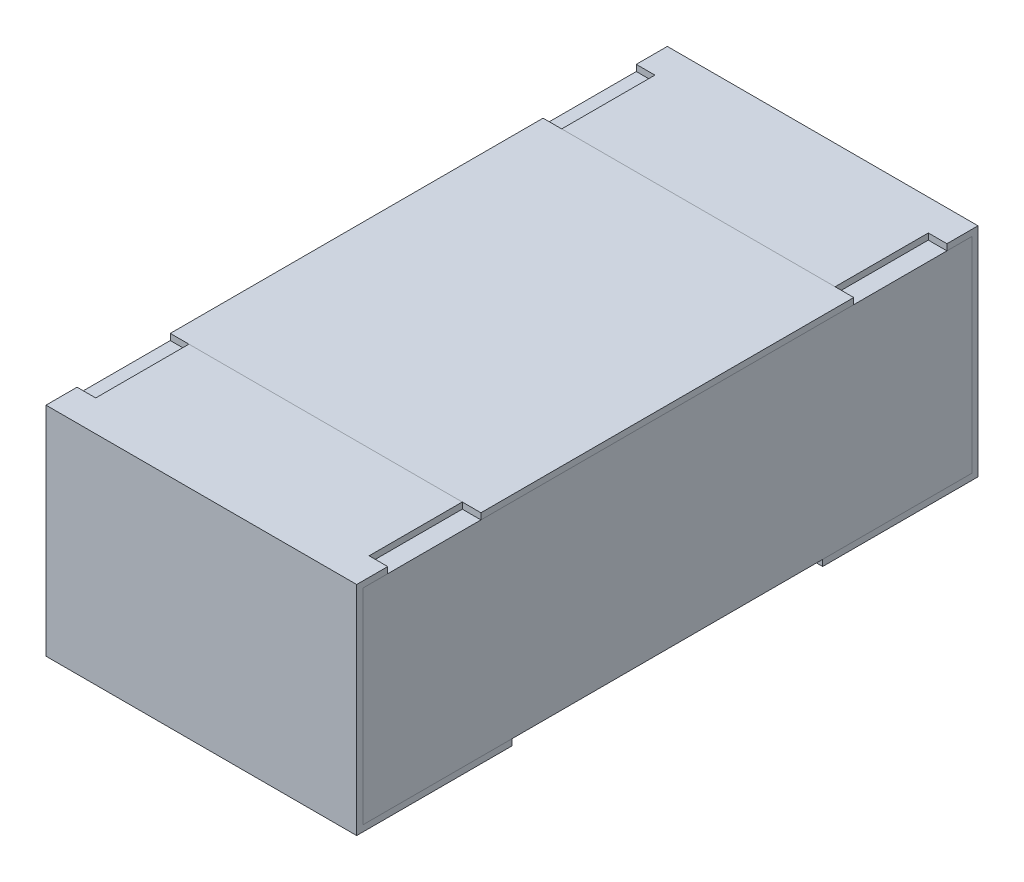
SolidWorks part; units mm, degrees
ref_plane "Front Plane" through (0, 0, 0) normal (0, 0, 1) x (1, 0, 0)
ref_plane "Top Plane" through (0, 0, 0) normal (0, 1, 0) x (1, 0, 0)
ref_plane "Right Plane" through (0, 0, 0) normal (1, 0, 0) x (0, 0, -1)
sketch "Sketch4" plane through (0, 0, 0) normal (1, 0, 0) x (0, 0, -1)
  line L0 (0, 0.1169) -> (0, -0.0721) construction
  line L1 (-0.5, 0) -> (0.3788, 0) construction
  line L2 (-0.5, 0.175) -> (-0.5, -0.175)
  line L3 (-0.5, -0.175) -> (-0.25, -0.175)
  line L4 (-0.3, 0.175) -> (-0.3, 0.165)
  line L5 (-0.3, 0.165) -> (-0.49, 0.165)
  line L6 (-0.49, 0.165) -> (-0.49, -0.165)
  line L7 (-0.49, -0.165) -> (-0.25, -0.165)
  line L8 (-0.25, -0.165) -> (-0.25, -0.175)
  line L9 (-0.3, 0.175) -> (-0.5, 0.175)
  line L10 (0.3, 0.175) -> (0.5, 0.175)
  line L11 (0.25, -0.165) -> (0.25, -0.175)
  line L12 (0.49, -0.165) -> (0.25, -0.165)
  line L13 (0.49, 0.165) -> (0.49, -0.165)
  line L14 (0.3, 0.165) -> (0.49, 0.165)
  line L15 (0.3, 0.175) -> (0.3, 0.165)
  line L16 (0.5, -0.175) -> (0.25, -0.175)
  line L17 (0.5, 0.175) -> (0.5, -0.175)
  dimension "LENGTH" = 0.5
  dimension "HEIGHT" = 0.35
  dimension "END CAP TOP LENGTH" = 0.2
  dimension "END CAP BOTTOM LENGTH" = 0.25
  dimension "D5" = 0.01
  dimension "D6" = 0.01
extrude "Boss-Extrude2" add sketch "Sketch4" along normal mid plane 0.5
sketch "Sketch5" plane through (0, 0, 0) normal (1, 0, 0) x (0, 0, -1)
  line L1 (-0.49, 0.165) -> (0.49, 0.165)
  line L2 (-0.49, 0.165) -> (-0.49, -0.165)
  line L3 (-0.49, -0.165) -> (0.49, -0.165)
  line L4 (0.49, 0.165) -> (0.49, -0.165)
extrude "Boss-Extrude3" add sketch "Sketch5" along normal up to surface and the other way up to surface separate body
sketch "Sketch6" plane through (0, 0.175, 0) normal (0, 1, 0) x (1, 0, 0)
  line L0 (-0.25, 0.5) -> (-0.25, 0.3) construction
  line L1 (-0.25, 0.45) -> (-0.22, 0.45)
  line L2 (-0.25, 0.45) -> (-0.25, 0.3)
  line L3 (-0.25, 0.3) -> (-0.22, 0.3)
  line L4 (-0.22, 0.45) -> (-0.22, 0.3)
  line L5 (0.25, 0.3) -> (-0.25, 0.3) construction
  line L6 (0, 0.0345) -> (0, -0.0345) construction
  line L7 (-0.0325, 0) -> (0.03, 0) construction
  line L8 (0.25, 0.45) -> (0.25, 0.3)
  line L9 (0.25, 0.3) -> (0.22, 0.3)
  line L10 (0.22, 0.45) -> (0.22, 0.3)
  line L11 (0.25, 0.45) -> (0.22, 0.45)
  line L12 (0.25, -0.45) -> (0.22, -0.45)
  line L13 (0.25, -0.45) -> (0.25, -0.3)
  line L14 (0.25, -0.3) -> (0.22, -0.3)
  line L15 (0.22, -0.45) -> (0.22, -0.3)
  line L16 (-0.25, -0.45) -> (-0.22, -0.45)
  line L17 (-0.25, -0.45) -> (-0.25, -0.3)
  line L18 (-0.25, -0.3) -> (-0.22, -0.3)
  line L19 (-0.22, -0.45) -> (-0.22, -0.3)
  dimension "TOP CUT WIDTH" = 0.03
  dimension "TOP CUT LENGTH" = 0.15
extrude "Cut-Extrude1" cut sketch "Sketch6" against normal up to surface (0.01 mm away) up to face at (0, 0.165, 0)
sketch "Sketch7" plane through (0, 0.165, 0) normal (0, 1, 0) x (1, 0, 0)
  line L1 (-0.25, 0.3) -> (0.25, 0.3)
  line L2 (-0.25, 0.3) -> (-0.25, -0.3)
  line L3 (-0.25, -0.3) -> (0.25, -0.3)
  line L4 (0.25, 0.3) -> (0.25, -0.3)
  line L5 (0.22, -0.3) -> (-0.22, -0.3) construction
  line L6 (0.22, 0.3) -> (-0.22, 0.3) construction
  line L7 (-0.25, -0.49) -> (-0.25, 0.49) construction
  line L8 (0.25, 0.49) -> (0.25, -0.49) construction
extrude "Boss-Extrude4" add sketch "Sketch7" along normal up to surface (0.01 mm away) separate body up to face at (0, 0.175, -0.425)
sketch "PART NUMBER" plane through (0, 0.175, 0) normal (0, 1, 0) x (1, 0, 0)
  line L0 (-0.0246, 0.1) -> (-0.0246, -0.1) construction
  line L1 (0, 0) -> (-0.0246, 0) construction
  text T0 "01005" font "Arial" height 0.05
  dimension "D1" = 0.2
extrude "TEXT01005" [suppressed] cut sketch "PART NUMBER" against normal blind 0.001
sketch "Sketch8" plane through (0, 0.175, 0) normal (0, 1, 0) x (1, 0, 0)
  line L0 (-0.0304, 0.1057) -> (-0.0304, -0.1057) construction
  line L1 (0, 0) -> (-0.0304, 0) construction
  text T0 "0201" font "Arial" height 0.06
extrude "TEXT0201" [suppressed] cut sketch "Sketch8" against normal blind 0.001
sketch "Sketch9" plane through (0, 0.175, 0) normal (0, 1, 0) x (1, 0, 0)
  line L0 (-0.0372, 0.139) -> (-0.0372, -0.139) construction
  line L1 (-0.0372, 0) -> (0, 0) construction
  text T0 "0402" font "Arial" height 0.08
extrude "TEXT0402" [suppressed] cut sketch "Sketch9" against normal blind 0.001
sketch "Sketch10" plane through (0, 0.175, 0) normal (0, 1, 0) x (1, 0, 0)
  line L0 (-0.125, 0.425) -> (-0.125, -0.425) construction
  line L1 (0, 0) -> (-0.125, 0) construction
  text T0 "0603" font "Arial" height 0.25
  dimension "D1" = 0.125
  dimension "D2" = 0.85
extrude "TEXT0603" [suppressed] cut sketch "Sketch10" against normal blind 0.001
sketch "Sketch11" plane through (0, 0.175, 0) normal (0, 1, 0) x (1, 0, 0)
  line L0 (0, 0) -> (-0.15, 0) construction
  line L1 (-0.15, 0.515) -> (-0.15, -0.515) construction
  text T0 "0805" font "Arial" height 0.3
  dimension "D1" = 0.15
extrude "TEXT0805" [suppressed] cut sketch "Sketch11" against normal blind 0.001
sketch "Sketch12" plane through (0, 0.175, 0) normal (0, 1, 0) x (1, 0, 0)
  line L0 (-0.15, 0.5423) -> (-0.15, -0.5423) construction
  line L1 (0, 0) -> (-0.15, 0) construction
  text T0 "1206" font "Arial" height 0.3
  dimension "D1" = 0.15
extrude "TEXT1206" [suppressed] cut sketch "Sketch12" against normal blind 0.001
sketch "Sketch13" plane through (0, 0.175, 0) normal (0, 1, 0) x (1, 0, 0)
  line L0 (-0.15, 0.5735) -> (-0.15, -0.5735) construction
  line L1 (0, 0) -> (-0.15, 0) construction
  text T0 "1210" font "Arial" height 0.3
  dimension "D1" = 0.15
extrude "TEXT1210" [suppressed] cut sketch "Sketch13" against normal blind 0.001
sketch "Sketch14" plane through (0, 0.175, 0) normal (0, 1, 0) x (1, 0, 0)
  line L0 (-0.25, 0.8778) -> (-0.25, -0.8778) construction
  line L1 (0, 0) -> (-0.25, 0) construction
  text T0 "1812" font "Arial" height 0.5
  dimension "D1" = 0.25
extrude "TEXT1812" [suppressed] cut sketch "Sketch14" against normal blind 0.001
sketch "Sketch15" plane through (0, 0.175, 0) normal (0, 1, 0) x (1, 0, 0)
  line L0 (-0.25, 0.9382) -> (-0.25, -0.9382) construction
  line L1 (0, 0) -> (-0.25, 0) construction
  text T0 "2010" font "Arial" height 0.5
  dimension "D1" = 0.25
extrude "TEXT2010" [suppressed] cut sketch "Sketch15" against normal blind 0.001
sketch "Sketch16" plane through (0, 0.175, 0) normal (0, 1, 0) x (1, 0, 0)
  line L0 (-0.25, 1.4279) -> (-0.25, -1.4279) construction
  line L1 (0, 0) -> (-0.25, 0) construction
  text T0 "2512" font "Arial" height 0.5
  dimension "D1" = 0.25
extrude "TEXT2512" [suppressed] cut sketch "Sketch16" against normal blind 0.001
